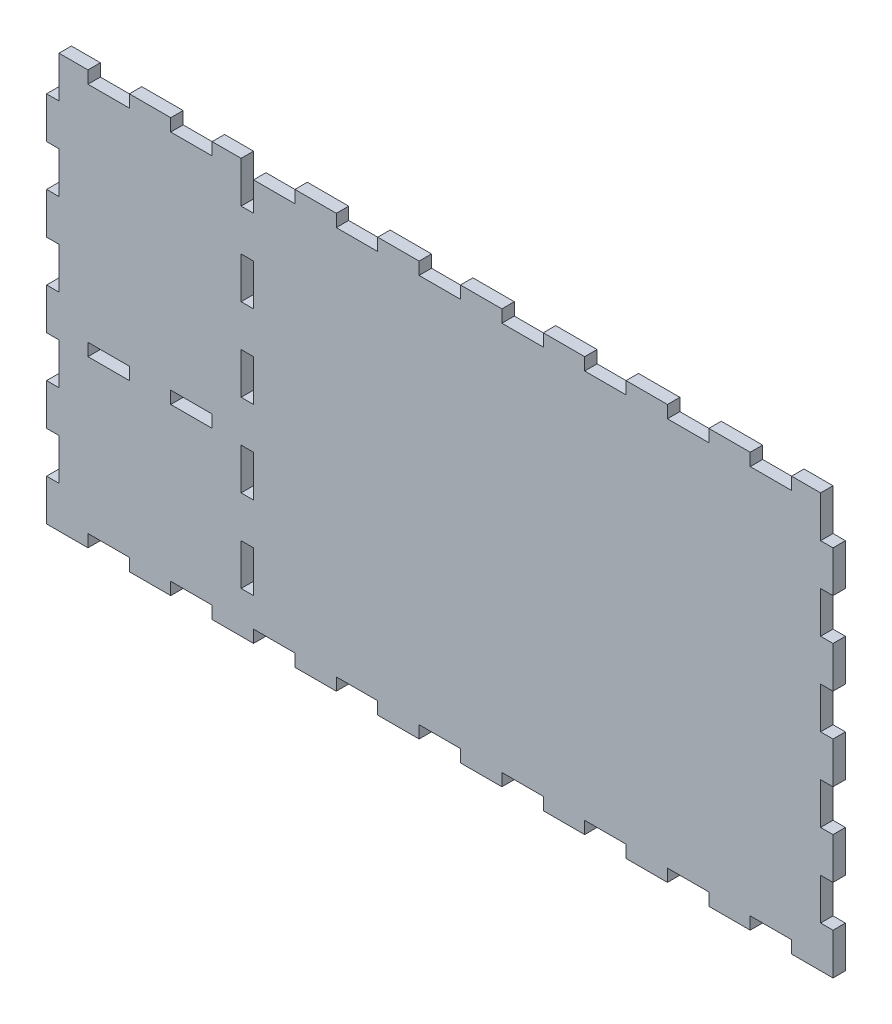
SolidWorks part; units mm, degrees
ref_plane "Front Plane" through (0, 0, 0) normal (0, 0, 1) x (1, 0, 0)
ref_plane "Top Plane" through (0, 0, 0) normal (0, 1, 0) x (1, 0, 0)
ref_plane "Right Plane" through (0, 0, 0) normal (1, 0, 0) x (0, 0, -1)
sketch "Sketch1" plane through (0, 0, 0) normal (0, 0, 1) x (1, 0, 0)
  line L2 (-112.9032, 78.2258) -> (-112.9032, -121.7742)
  line L20 (-112.9032, -121.7742) -> (267.0968, -121.7742)
  line L21 (267.0968, -121.7742) -> (267.0968, 78.2258)
  line L22 (-112.9032, 78.2258) -> (267.0968, 78.2258)
  dimension "D1" = 380
  dimension "D2" = 200
extrude "Boss-Extrude1" add sketch "Sketch1" along normal blind 6
sketch "Sketch6" plane through (0, 0, 0) normal (0, 0, 1) x (1, 0, 0)
  line L1 (-112.9032, 78.2258) -> (-106.9032, 78.2258)
  line L2 (-112.9032, 78.2258) -> (-112.9032, 58.2258)
  line L3 (-112.9032, 58.2258) -> (-106.9032, 58.2258)
  line L4 (-106.9032, 78.2258) -> (-106.9032, 58.2258)
  dimension "D1" = 6
  dimension "D2" = 20
extrude "Cut-Extrude4" cut sketch "Sketch6" along normal through all
pattern_linear "LPattern3" count 5 spacing 40 along (0, -1, 0) of "Cut-Extrude4"
sketch "Sketch7" plane through (0, 0, 6) normal (0, 0, 1) x (1, 0, 0)
  line L0 (267.0968, 78.2258) -> (-106.9032, 78.2258) construction
  line L1 (-92.9032, 78.2258) -> (-72.9032, 78.2258)
  line L2 (-92.9032, 78.2258) -> (-92.9032, 72.2258)
  line L3 (-92.9032, 72.2258) -> (-72.9032, 72.2258)
  line L4 (-72.9032, 78.2258) -> (-72.9032, 72.2258)
  line L5 (-112.9032, 58.2258) -> (-112.9032, 38.2258) construction
  dimension "D1" = 6
  dimension "D2" = 20
  dimension "D3" = 20
extrude "Cut-Extrude5" cut sketch "Sketch7" against normal blind 10
pattern_linear "LPattern4" count 9 spacing 40 along (1, 0, 0) of "Cut-Extrude5"
sketch "Sketch8" plane through (0, 0, 6) normal (0, 0, 1) x (1, 0, 0)
  line L0 (267.0968, -21.7742) -> (-128.9461, -21.7742)
  line L1 (267.0968, -121.7742) -> (267.0968, 78.2258) construction
ref_plane "Plane1" through (0, -21.7742, 0) normal (0, 1, 0) x (-1, 0, 0)
mirror "Mirror1" about plane through (0, -21.7742, 0) normal (0, 1, 0) of "LPattern4", "Cut-Extrude5"
sketch "Sketch9" plane through (0, 0, 6) normal (0, 0, 1) x (1, 0, 0)
  line L0 (77.0968, -192.3343) -> (77.0968, 107.6657)
  line L1 (267.0968, -121.7742) -> (267.0968, 78.2258) construction
  line L2 (-112.9032, 58.2258) -> (-112.9032, 38.2258) construction
  line L3 (-112.9032, -101.7742) -> (-112.9032, -121.7742) construction
  dimension "D1" = 190
  dimension "D2" = 190
  dimension "D3" = 300
  dimension "D4" = 190
ref_plane "Plane2" through (77.0968, 0, 0) normal (1, 0, 0) x (0, 1, 0)
mirror "Mirror2" about plane through (77.0968, 0, 0) normal (1, 0, 0) of "LPattern3", "Cut-Extrude4"
sketch "Sketch10" plane through (0, 0, 0) normal (0, 0, -1) x (-1, 0, 0)
  line L0 (12.9032, 78.2258) -> (12.9032, 72.2258) construction
  line L1 (12.9032, 58.2258) -> (18.9032, 58.2258)
  line L2 (12.9032, 58.2258) -> (12.9032, 78.2258)
  line L3 (12.9032, 78.2258) -> (18.9032, 78.2258)
  line L4 (18.9032, 58.2258) -> (18.9032, 78.2258)
  point P5 (-167.0968, 46.6907)
  point P6 (32.9032, 78.2258)
  point P8 (-167.0968, -121.7742)
  dimension "D1" = 6
  dimension "D2" = 20
  dimension "D3" = 0
extrude "Cut-Extrude6" cut sketch "Sketch10" against normal blind 10
pattern_linear "LPattern5" count 5 spacing 40 along (0, -1, 0) of "Cut-Extrude6"
sketch "Sketch11" plane through (0, 0, 0) normal (0, 0, -1) x (-1, 0, 0)
  line L0 (18.9032, -41.7742) -> (12.9032, -41.7742) construction
  line L1 (32.9032, -35.7742) -> (52.9032, -35.7742)
  line L2 (32.9032, -35.7742) -> (32.9032, -41.7742)
  line L3 (32.9032, -41.7742) -> (52.9032, -41.7742)
  line L4 (52.9032, -35.7742) -> (52.9032, -41.7742)
  line L6 (12.9032, -41.7742) -> (12.9032, -61.7742) construction
  dimension "D1" = 0
  dimension "D2" = 6
  dimension "D3" = 20
  dimension "D4" = 20
extrude "Cut-Extrude7" cut sketch "Sketch11" against normal blind 10 contours L1 L4 L3 L2
pattern_linear "LPattern6" count 2 spacing 40 along (-1, 0, 0) of "Cut-Extrude7"
